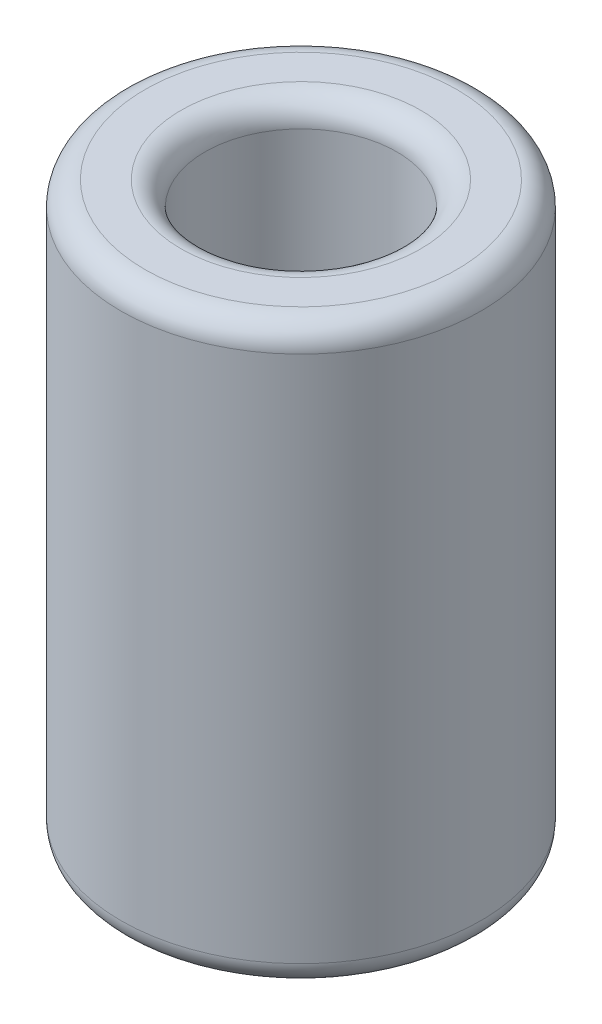
SolidWorks part; units mm, degrees
ref_plane "Front Plane" through (0, 0, 0) normal (0, 0, 1) x (1, 0, 0)
ref_plane "Top Plane" through (0, 0, 0) normal (0, 1, 0) x (1, 0, 0)
ref_plane "Right Plane" through (0, 0, 0) normal (1, 0, 0) x (0, 0, -1)
sketch "Sketch1" plane through (0, 0, 0) normal (0, 1, 0) x (1, 0, 0)
  circle A0 centre (0, 0) radius 4
  circle A1 centre (0, 0) radius 7.5
  dimension "D1" = 8
  dimension "D2" = 15
extrude "Boss-Extrude1" add sketch "Sketch1" along normal blind 24
fillet "Fillet2" radius 1 4 edges at (0, 0, 4) (0, 24, 4) (0, 0, 7.5) (0, 24, 7.5)
